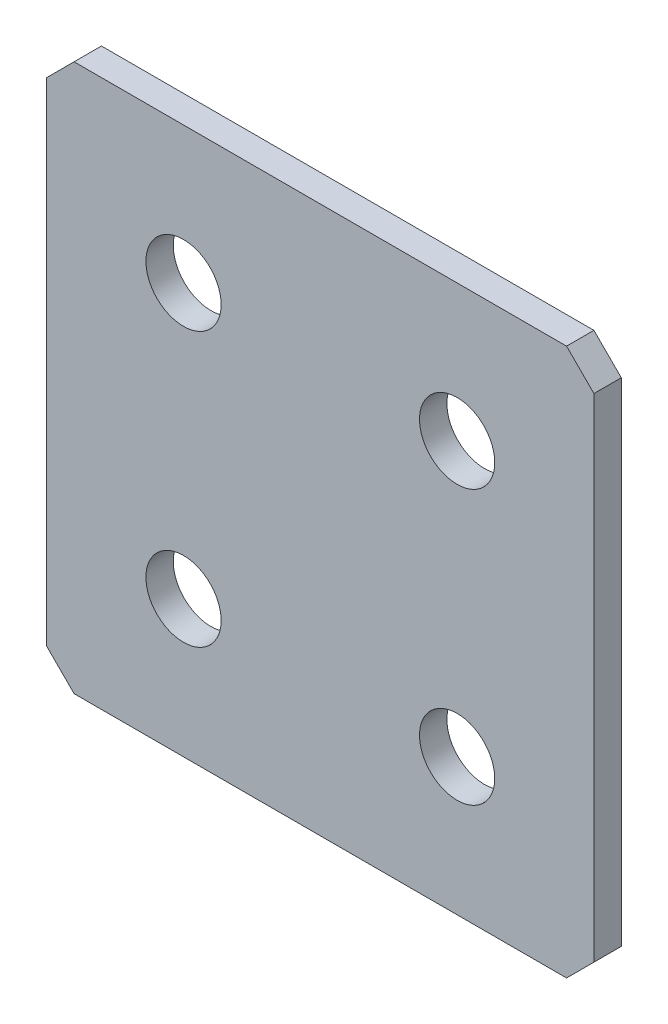
SolidWorks part; units mm, degrees
material "Простая углеродистая сталь"
ref_plane "Спереди(Плоскость XY)" through (0, 0, 0) normal (0, 0, 1) x (1, 0, 0)
ref_plane "Сверху(Плоскость XZ)" through (0, 0, 0) normal (0, 1, 0) x (1, 0, 0)
ref_plane "Справа(Плоскость ZY)" through (0, 0, 0) normal (1, 0, 0) x (0, 0, -1)
sketch "Эскиз1" plane through (0, 0, 0) normal (0, 0, 1) x (1, 0, 0)
  line L1 (-20, -20) -> (20, -20)
  line L2 (-20, -20) -> (-20, 20)
  line L3 (-20, 20) -> (20, 20)
  line L4 (20, -20) -> (20, 20)
  line L5 (-20, -20) -> (20, 20) construction
  line L6 (-20, 20) -> (20, -20) construction
  point P0 (0, 0)
  dimension "D1" = 40
  dimension "D2" = 40
extrude "Бобышка-Вытянуть1" add sketch "Эскиз1" along normal blind 2
chamfer "Фаска1" distance 2 angle 45 4 edges at (-20, -20, 1) (20, -20, 1) (-20, 20, 1) (20, 20, 1)
hole_wizard "Отверстие с зазором M51" positions "Эскиз2" profile "Эскиз3" hole size "M5" standard "DIN" end condition through all
sketch "Эскиз2" plane through (0, 0, 2) normal (0, 0, 1) x (1, 0, 0)
  line L2 (-10, 10) -> (10, 10) construction
  line L3 (-10, 10) -> (-10, 30) construction
  line L4 (-10, 30) -> (10, 30) construction
  line L5 (10, 10) -> (10, 30) construction
  line L7 (-10, -10) -> (10, -10) construction
  line L8 (-10, -10) -> (-10, -30) construction
  line L9 (-10, -30) -> (10, -30) construction
  line L10 (10, -10) -> (10, -30) construction
  line L11 (0, 10) -> (0, -10) construction
  point P0 (-10, 10)
  point P2 (10, 10)
  point P8 (-10, -10)
  point P10 (10, -10)
  point P22 (-10, 30)
  point P24 (10, 30)
  point P93 (10, -30)
  point P170 (-10, -30)
  dimension "D1" = 20
  dimension "D2" = 20
  dimension "D3" = 20
sketch "Эскиз3" plane through (-10, 10, 2) normal (1, 0, 0) x (0, -1, 0)
  line L0 (0, 0) -> (0, 2)
  line L1 (0, 2) -> (2.75, 2)
  line L2 (2.75, 2) -> (2.75, 0)
  line L5 (2.75, 0) -> (0, 0)
  line L11 (0, -6.35) -> (0, 107.95) construction
  dimension "Диаметр сквозного отверстия" = 5.5
  dimension "Глубина сквозного отверстия" = 2
